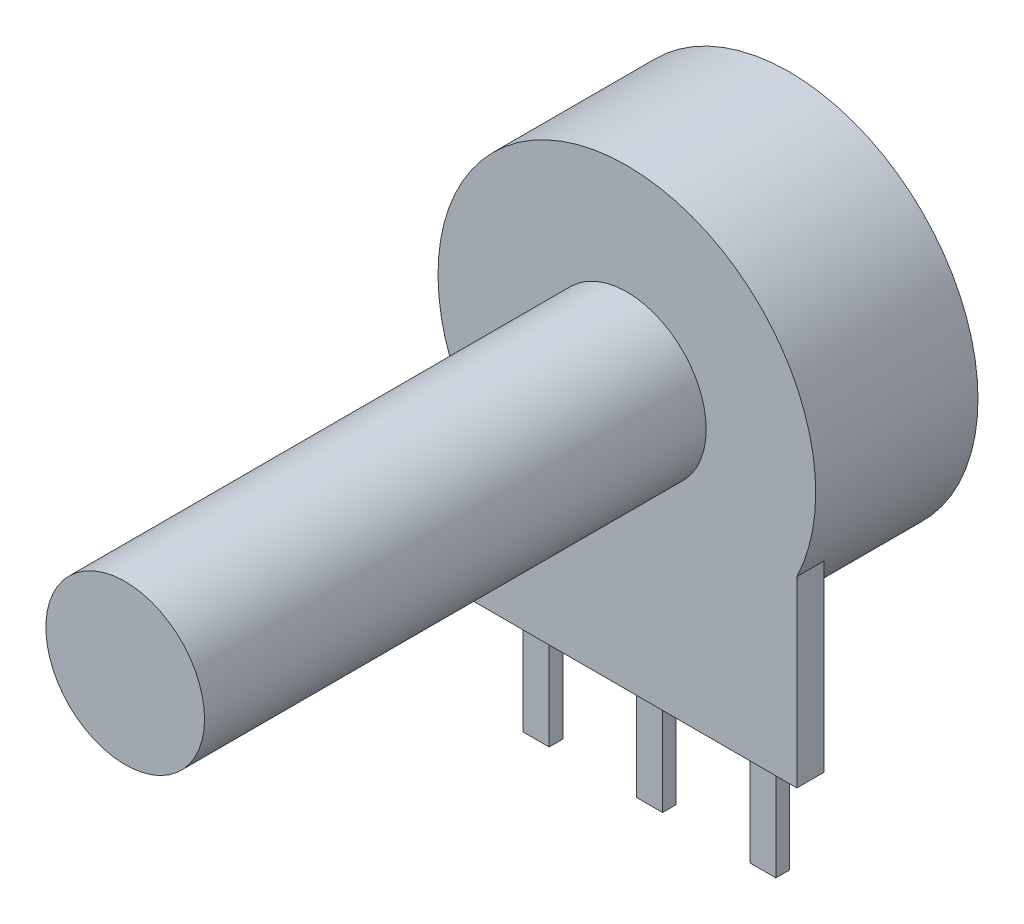
SolidWorks part; units mm, degrees
ref_plane "Front Plane" through (0, 0, 0) normal (0, 0, 1) x (1, 0, 0)
ref_plane "Top Plane" through (0, 0, 0) normal (0, 1, 0) x (1, 0, 0)
ref_plane "Right Plane" through (0, 0, 0) normal (1, 0, 0) x (0, 0, -1)
sketch "Sketch1" plane through (0, 0, 0) normal (0, 0, 1) x (1, 0, 0)
  circle A0 centre (0, 0) radius 8.33
  dimension "D1" = 16.66
extrude "Boss-Extrude1" add sketch "Sketch1" along normal blind 7.16
sketch "Sketch2" plane through (0, 0, 7.16) normal (0, 0, 1) x (1, 0, 0)
  circle A0 centre (0, 0) radius 3.5
  dimension "D1" = 7
extrude "Boss-Extrude2" add sketch "Sketch2" along normal blind 22.13
sketch "Sketch3" plane through (0, 0, 7.16) normal (0, 0, 1) x (1, 0, 0)
  line L1 (-7.5, -11.7) -> (7.5, -11.7)
  line L2 (-7.5, -11.7) -> (-7.5, -0.4955)
  line L3 (-7.5, -0.4955) -> (7.5, -0.4955)
  line L4 (7.5, -11.7) -> (7.5, -0.4955)
  line L5 (0, -0.4955) -> (0, -11.7) construction
  line L6 (-7.5, -6.0977) -> (7.5, -6.0977) construction
  circle A0 centre (0, 0) radius 8.33 construction
  point P0 (0, -6.0977)
  dimension "D1" = 15
  dimension "D2" = 11.7
extrude "Boss-Extrude3" add sketch "Sketch3" against normal blind 1.2
sketch "Sketch4" plane through (0, 0, 5.96) normal (0, 0, -1) x (-1, 0, 0)
  line L0 (0, -8.33) -> (0, -11.7) construction
  line L1 (7.5, -11.7) -> (-7.5, -11.7) construction
  line L2 (-0.575, -11.7) -> (0.575, -11.7)
  line L3 (-0.575, -6.8) -> (0.575, -6.8)
  line L4 (-0.575, -6.8) -> (-0.575, -16.6)
  line L5 (-0.575, -16.6) -> (0.575, -16.6)
  line L6 (0.575, -6.8) -> (0.575, -16.6)
  line L7 (0, -16.6) -> (0, -6.8) construction
  line L8 (-0.575, -11.7) -> (0.575, -11.7) construction
  arc A0 (-7.5, -3.6248) -> (7.5, -3.6248) centre (0, 0) ccw construction
  line M4 (-7.5, -11.7) -> (7.5, -11.7)
  dimension "D1" = 1.15
  dimension "D2" = 4.9
extrude "Boss-Extrude4" add sketch "Sketch4" along normal blind 0.6 from offset 0.2 contours L6 L4 L5 M4 offset against normal yes
pattern_linear "LPattern1" count 2 spacing 5 along (1, 0, 0) count 2 spacing 5 along (-1, 0, 0) of "Boss-Extrude4"
